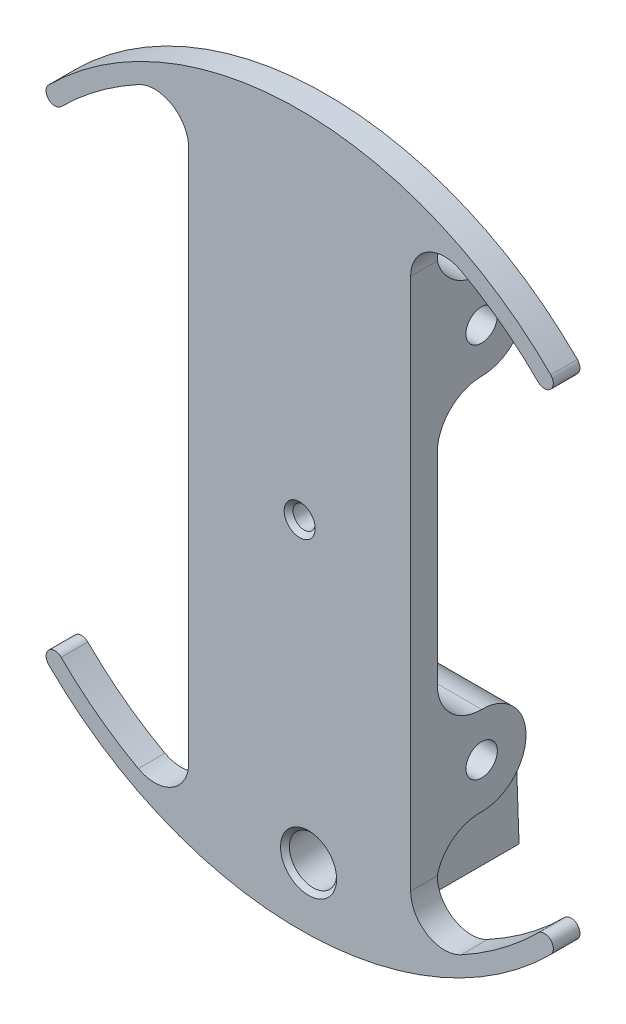
SolidWorks part; units mm, degrees
ref_plane "Front Plane" through (0, 0, 0) normal (0, 0, 1) x (1, 0, 0)
ref_plane "Top Plane" through (0, 0, 0) normal (0, 1, 0) x (1, 0, 0)
ref_plane "Right Plane" through (0, 0, 0) normal (1, 0, 0) x (0, 0, -1)
sketch "Sketch3" plane through (0, 0, 0) normal (0, 0, 1) x (1, 0, 0)
  line L0 (-35.921, -35.921) -> (-34.125, -34.125) construction
  line L1 (-15.875, -38.1) -> (0, -38.1) construction
  line L2 (-15.875, -38.1) -> (-15.875, 38.1)
  line L3 (-15.875, 38.1) -> (0, 38.1) construction
  line L4 (15.875, -38.1) -> (15.875, 38.1)
  line L5 (-15.875, -38.1) -> (15.875, 38.1) construction
  line L6 (-15.875, 38.1) -> (15.875, -38.1) construction
  line L7 (35.921, -35.921) -> (34.125, -34.125) construction
  line L8 (0, -50.8) -> (0, 50.8) construction
  line L9 (0, 38.1) -> (15.875, 38.1) construction
  line L10 (0, -38.1) -> (15.875, -38.1) construction
  line L11 (-34.125, -34.125) -> (-15.875, -15.875) construction
  line L12 (34.125, 34.125) -> (35.921, 35.921) construction
  line L13 (-15.875, -15.875) -> (0, 0) construction
  line L14 (15.875, -15.875) -> (0, 0) construction
  line L15 (-34.125, 34.125) -> (-35.921, 35.921) construction
  line L16 (34.125, -34.125) -> (15.875, -15.875) construction
  line L17 (0, 0) -> (-15.875, 15.875) construction
  line L18 (0, 0) -> (15.875, 15.875) construction
  line L19 (-15.875, 15.875) -> (-34.125, 34.125) construction
  line L20 (15.875, 15.875) -> (34.125, 34.125) construction
  arc A0 (-35.921, -35.921) -> (35.921, -35.921) centre (0, 0) ccw
  arc A1 (-34.125, -34.125) -> (-23.0827, -42.3818) centre (0, 0) ccw
  arc A2 (-15.875, 38.1) -> (-23.0827, 42.3818) centre (-20.7507, 38.1) ccw
  arc A3 (15.875, 38.1) -> (23.0827, 42.3818) centre (20.7507, 38.1) cw
  arc A4 (-15.875, -38.1) -> (-23.0827, -42.3818) centre (-20.7507, -38.1) cw
  arc A5 (15.875, -38.1) -> (23.0827, -42.3818) centre (20.7507, -38.1) ccw
  arc A6 (-35.921, 35.921) -> (-35.921, -35.921) centre (0, 0) ccw construction
  circle A7 centre (0, 0) radius 50.8 construction
  arc A8 (-34.125, 34.125) -> (-34.125, -34.125) centre (0, 0) ccw construction
  circle A9 centre (0, 0) radius 48.26 construction
  arc A10 (34.125, -34.125) -> (34.125, 34.125) centre (0, 0) ccw construction
  arc A11 (34.125, 34.125) -> (23.0827, 42.3818) centre (0, 0) ccw
  arc A12 (35.921, -35.921) -> (35.921, 35.921) centre (0, 0) ccw construction
  arc A13 (35.921, 35.921) -> (-35.921, 35.921) centre (0, 0) ccw
  arc A14 (0, 48.26) -> (-23.0827, 42.3818) centre (0, 0) ccw construction
  arc A15 (-23.0827, 42.3818) -> (-34.125, 34.125) centre (0, 0) ccw
  arc A16 (23.0827, 42.3818) -> (0, 48.26) centre (0, 0) ccw construction
  arc A17 (-23.0827, -42.3818) -> (0, -48.26) centre (0, 0) ccw construction
  arc A18 (23.0827, -42.3818) -> (34.125, -34.125) centre (0, 0) ccw
  arc A19 (0, -48.26) -> (23.0827, -42.3818) centre (0, 0) ccw construction
  arc A20 (-35.921, 35.921) -> (-34.125, 34.125) centre (-35.023, 35.023) ccw
  arc A21 (34.125, 34.125) -> (35.921, 35.921) centre (35.023, 35.023) ccw
  arc A22 (-35.921, -35.921) -> (-34.125, -34.125) centre (-35.023, -35.023) cw
  arc A23 (34.125, -34.125) -> (35.921, -35.921) centre (35.023, -35.023) cw
  point P0 (0, 0)
  point P13 (0, 0)
  point P16 (0, 0)
  point P18 (0, 0)
  dimension "D3" = 2.54
  dimension "D6" = 101.6
  dimension "D1" = 76.2
  dimension "D2" = 31.75
  dimension "D4" = 45
  dimension "D5" = 45
extrude "Boss-Extrude2" add sketch "Sketch3" along normal blind 3.81
sketch "Sketch5" plane through (15.875, 0, 0) normal (1, 0, 0) x (0, 0, -1)
  line L0 (0, 26.9938) -> (0, -26.9938)
  line L1 (0, -38.1) -> (0, 38.1) construction
  line L2 (0, 26.9938) -> (6.35, 26.9939) construction
  line L3 (6.35, 26.9939) -> (6.35, -26.9938) construction
  line L4 (6.35, -26.9938) -> (0, -26.9938) construction
  line L5 (0, 38.1) -> (0, 14.2939)
  line L6 (0, -14.2939) -> (0, -38.1)
  circle A0 centre (-0.0451, 26.9938) radius 0.0451
  arc A2 (6.35, 20.6439) -> (6.3413, 33.3438) centre (6.35, 26.9939) ccw
  arc A3 (6.0778, -33.338) -> (6.2617, -20.6445) centre (6.35, -26.9938) ccw
  arc A4 (6.35, 20.6439) -> (0, 14.2939) centre (6.3675, 14.2763) ccw
  arc A5 (6.3413, 33.3438) -> (0, 38.1) centre (6.1542, 39.6999) cw
  arc A6 (6.35, -20.6438) -> (0, -14.2939) centre (6.2623, -14.3815) cw
  arc A7 (6.35, -33.3439) -> (0, -38.1) centre (6.0797, -39.6) ccw
  arc A8 (6.3413, 33.3438) -> (0, 26.9938) centre (6.35, 26.9939) ccw construction
  arc A9 (0, 26.9938) -> (6.35, 20.6439) centre (6.35, 26.9939) ccw construction
  arc A10 (6.2617, -20.6445) -> (0, -26.9938) centre (6.35, -26.9938) ccw construction
  arc A11 (0, -26.9938) -> (6.0778, -33.338) centre (6.35, -26.9938) ccw construction
  point P5 (0, 0)
  line M6 (0, -38.1) -> (0, 38.1)
  dimension "D1" = 53.9877
  dimension "D2" = 6.35
  dimension "D3" = 12.7
  dimension "D4" = 12.7
extrude "Boss-Extrude4" add sketch "Sketch5" against normal up to surface (31.75 mm away) contours A2 A5 L0 A4 M6 | A7 A3 A6 L6 M6 up to face at (-15.875, 0, 1.905)
sketch "Sketch18" plane through (0, 0, 0) normal (0, 0, -1) x (-1, 0, 0)
  line L1 (-10.4707, -49.4103) -> (9.3869, -49.4103)
  line L2 (-10.4707, -49.4103) -> (-10.4707, -34.1772)
  line L3 (-10.4707, -34.1772) -> (9.3869, -34.1772)
  line L4 (9.3869, -49.4103) -> (9.3869, -34.1772)
extrude "Boss-Extrude6" [suppressed] add sketch "Sketch18" along normal blind 25.4
hole_wizard "#8 Clearance Hole1" positions "Sketch8" profile "Sketch7" hole size "#8" standard "ANSI Inch" end condition through all
sketch "Sketch8" plane through (15.875, 0, 0) normal (1, 0, 0) x (0, 0, -1)
  point P7 (6.35, 26.9939)
  point P10 (6.35, -26.8934)
sketch "Sketch7" plane through (15.875, 26.9939, -6.35) normal (0, 1, 0) x (0, 0, -1)
  line L0 (0, 0) -> (0, 52.168)
  line L1 (0, 52.168) -> (2.2479, 52.168)
  line L2 (2.2479, 52.168) -> (2.2479, 0)
  line L5 (2.2479, 0) -> (0, 0)
  line L11 (0, -6.35) -> (0, 107.95) construction
  dimension "Thru Hole Dia." = 4.4958
  dimension "Thru Hole Depth" = 52.168
hole_wizard "1/8 (0.125) Diameter Hole1" positions "Sketch9" profile "Sketch10" hole size "1/8" standard "ANSI Inch" end condition up to next
sketch "Sketch9" plane through (0, 0, 0) normal (0, 0, -1) x (-1, 0, 0)
  point P0 (0, 0)
sketch "Sketch10" plane through (0, 0, 0) normal (1, 0, 0) x (0, 1, 0)
  line L0 (0, 0) -> (0, 3.81)
  line L1 (0, 3.81) -> (2.2225, 3.81)
  line L2 (1.5875, 3.175) -> (1.5875, 0.635)
  line L3 (1.5875, 0.635) -> (2.2225, 0)
  line L5 (2.2225, 0) -> (0, 0)
  line L6 (-1.5875, 0.635) -> (-2.2225, 0) construction
  line L7 (2.2225, 3.81) -> (1.5875, 3.175)
  line L8 (-2.2225, 3.81) -> (-1.5875, 3.175) construction
  line L11 (0, -6.35) -> (0, 107.95) construction
  dimension "Thru Hole Dia." = 3.175
  dimension "Thru Hole Depth" = 3.81
  dimension "Near C'Sink Dia." = 4.445
  dimension "Near C'Sink Angle" = 90
  dimension "Far C'Sink Dia." = 4.445
  dimension "Far C'Sink Angle" = 90
sketch "Sketch19" plane through (0, 0, 0) normal (0, 0, -1) x (-1, 0, 0)
  line L0 (12.7, -38.735) -> (3.175, -38.735)
  line L1 (-1.27, 0) -> (0, 0) construction
  line L4 (3.175, -38.735) -> (3.175, -45.085)
  line L6 (-1.27, -41.91) -> (-1.27, 0) construction
  line L12 (12.7, -48.26) -> (-7.62, -48.26)
  line L13 (-7.62, -48.26) -> (-7.62, -35.56)
  line L14 (-7.62, -35.56) -> (12.7, -35.56)
  line L16 (12.7, -38.735) -> (12.7, -35.56)
  line L18 (12.7, -45.085) -> (12.7, -48.26)
  line L25 (3.175, -45.085) -> (12.7, -45.085)
  line L26 (-1.27, -41.91) -> (3.175, -41.91) construction
  circle A1 centre (-1.27, -41.91) radius 3.3782
  dimension "D1" = 4.445
  dimension "D2" = 3.175
  dimension "D3" = 20.32
  dimension "D4" = 6.35
  dimension "D5" = 3.175
  dimension "D6" = 6.35
  dimension "D7" = 12.7
  dimension "D8" = 41.91
  dimension "D9" = 1.27
extrude "Boss-Extrude7" add sketch "Sketch19" along normal up to surface (19.9395 mm away)
hole_wizard "1/4 Clearance Hole3" positions "Sketch23" profile "Sketch24" hole size "1/4" standard "ANSI Inch" end condition through all
sketch "Sketch23" plane through (0, 0, 3.81) normal (0, 0, 1) x (1, 0, 0)
  line L16 (-12.7, -38.735) -> (-3.175, -38.735)
  line L17 (-3.175, -38.735) -> (-3.175, -45.085)
  line L18 (-3.175, -45.085) -> (-12.7, -45.085)
  line L19 (-12.7, -45.085) -> (-12.7, -48.26)
  line L20 (-12.7, -48.26) -> (7.62, -48.26)
  line L21 (7.62, -48.26) -> (7.62, -35.56)
  line L22 (7.62, -35.56) -> (-12.7, -35.56)
  line L23 (-12.7, -35.56) -> (-12.7, -38.735)
  line L24 (-12.7, -38.735) -> (-3.175, -38.735)
  line L25 (-3.175, -38.735) -> (-3.175, -45.085)
  line L26 (-3.175, -45.085) -> (-12.7, -45.085)
  line L27 (-12.7, -45.085) -> (-12.7, -48.26)
  line L28 (-12.7, -48.26) -> (7.62, -48.26)
  line L29 (7.62, -48.26) -> (7.62, -35.56)
  line L30 (7.62, -35.56) -> (-12.7, -35.56)
  line L31 (-12.7, -35.56) -> (-12.7, -38.735)
  circle A2 centre (1.27, -41.91) radius 3.3782
  circle A3 centre (1.27, -41.91) radius 3.3782
  point P39 (1.27, -41.91)
  dimension "D1" = 0
  dimension "D2" = 0
sketch "Sketch24" plane through (1.27, -41.91, 3.81) normal (1, 0, 0) x (0, -1, 0)
  line L0 (0, 0) -> (0, 23.9403)
  line L1 (0, 23.9403) -> (3.3782, 23.9403)
  line L2 (3.3782, 23.9403) -> (3.3782, 0.635)
  line L3 (3.3782, 0.635) -> (4.0132, 0)
  line L5 (4.0132, 0) -> (0, 0)
  line L6 (-3.3782, 0.635) -> (-4.0132, 0) construction
  line L11 (0, -6.35) -> (0, 107.95) construction
  dimension "Thru Hole Dia." = 6.7564
  dimension "Thru Hole Depth" = 23.9403
  dimension "Near C'Sink Dia." = 8.0264
  dimension "Near C'Sink Angle" = 90
sketch "Sketch25" plane through (-3.175, 0, 0) normal (-1, 0, 0) x (0, 0, 1)
  line L0 (-20.1303, -48.26) -> (0, -48.26) construction
  line L1 (0, -45.085) -> (0, -38.735) construction
  circle A0 centre (-7.62, -41.91) radius 2.794
  dimension "D2" = 5.588
  dimension "D1" = 6.35
  dimension "D3" = 7.62
extrude "Cut-Extrude1" cut sketch "Sketch25" against normal blind 3.81
sketch "Sketch28" plane through (0, -48.26, 0) normal (0, -1, 0) x (-1, 0, 0)
  line L0 (9.825, 5.35) -> (9.825, 5.05) construction
hole_wizard "#2 Clearance Hole1" positions "Sketch29" profile "Sketch30" hole size "#2" standard "ANSI Inch"
sketch "Sketch29" plane through (0, -48.26, 0) normal (0, -1, 0) x (-1, 0, 0)
  line L0 (9.825, 5.35) -> (9.825, 5.05) construction
  point P0 (9.825, 14.7)
  point P13 (9.825, 5.2)
  point P16 (0, 0)
  point P17 (0, 0)
sketch "Sketch30" plane through (-9.825, -48.26, -14.7) normal (1, 0, 0) x (0, 0, -1)
  line L0 (0, 0) -> (0, 3.175)
  line L1 (0, 3.175) -> (1.2192, 3.175)
  line L2 (1.2192, 3.175) -> (1.2192, 0)
  line L5 (1.2192, 0) -> (0, 0)
  line L11 (0, -6.35) -> (0, 107.95) construction
  dimension "Thru Hole Dia." = 2.4384
  dimension "Thru Hole Depth" = 3.175
hole_wizard "Tap Drill for #2-56 Tap1" positions "Sketch31" profile "Sketch32" hole size "#2-56" standard "ANSI Inch"
sketch "Sketch31" plane through (0, -48.26, 0) normal (0, -1, 0) x (-1, 0, 0)
  line L0 (9.825, 5.35) -> (9.825, 5.05) construction
  point P0 (9.825, 14.7)
  point P3 (9.825, 5.2)
sketch "Sketch32" plane through (-9.825, -48.26, -14.7) normal (1, 0, 0) x (0, 0, -1)
  line L0 (0, 0) -> (0, 12.7)
  line L1 (0, 12.7) -> (0.889, 12.7)
  line L2 (0.889, 12.7) -> (0.889, 0)
  line L5 (0.889, 0) -> (0, 0)
  line L11 (0, -6.35) -> (0, 107.95) construction
  dimension "Thru Hole Dia." = 1.778
  dimension "Thru Hole Depth" = 12.7
